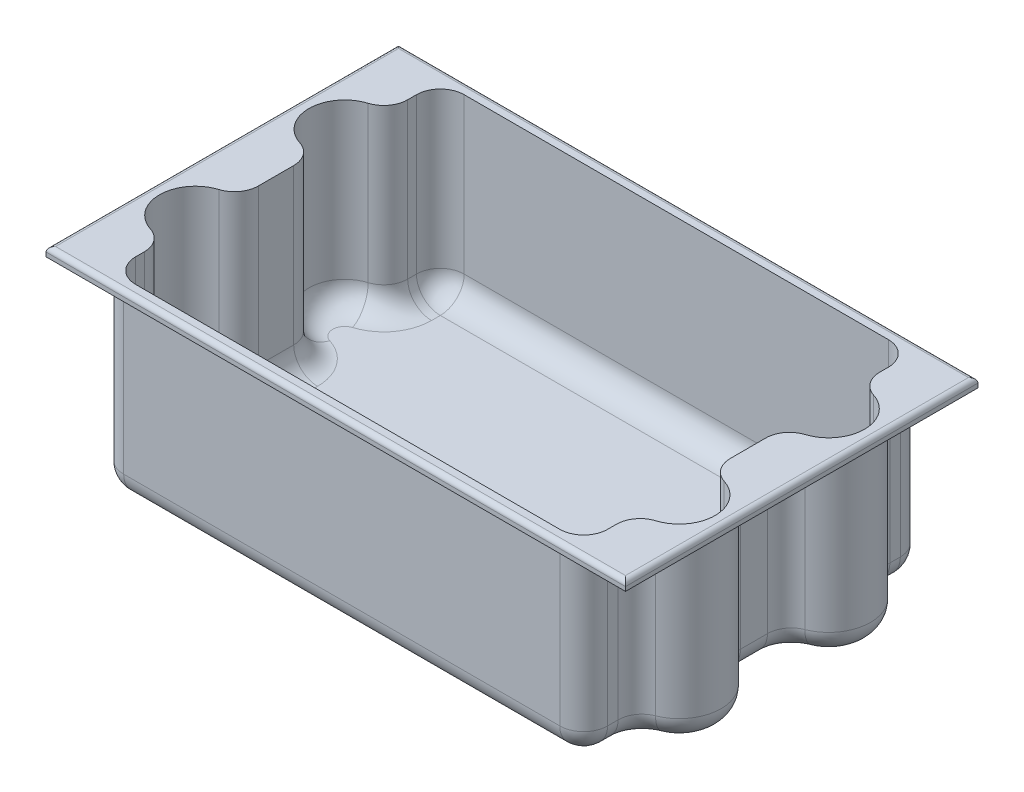
SolidWorks part; units mm, degrees
ref_plane "Front Plane" through (0, 0, 0) normal (0, 0, 1) x (1, 0, 0)
ref_plane "Top Plane" through (0, 0, 0) normal (0, 1, 0) x (1, 0, 0)
ref_plane "Right Plane" through (0, 0, 0) normal (1, 0, 0) x (0, 0, -1)
sketch "Sketch1" plane through (0, 0, 0) normal (0, 1, 0) x (1, 0, 0)
  line L0 (0, 0) -> (0, 50000) construction
  line L1 (-307.975, 187.325) -> (307.975, 187.325)
  line L2 (-307.975, 187.325) -> (-307.975, -187.325)
  line L3 (-307.975, -187.325) -> (307.975, -187.325)
  line L4 (307.975, 187.325) -> (307.975, -187.325)
  line L5 (0, -55) -> (0, 55) construction
  line L6 (0, 0) -> (50000, 0) construction
  line L7 (-55, 0) -> (55, 0) construction
  dimension "D1" = 615.95
  dimension "D2" = 374.65
extrude "Boss-Extrude1" add sketch "Sketch1" along normal blind 200.025
sketch "Sketch2" plane through (0, 0, 0) normal (0, -1, 0) x (1, 0, 0)
  line L0 (0, 0) -> (0, 50000) construction
  line L1 (-257.175, 174.625) -> (257.175, 174.625) construction
  line L2 (-257.175, 174.625) -> (-257.175, -174.625) construction
  line L3 (-257.175, -174.625) -> (257.175, -174.625) construction
  line L4 (257.175, 174.625) -> (257.175, -174.625) construction
  line L5 (0, -110.0137) -> (0, 110.0137) construction
  line L6 (0, 0) -> (50000, 0) construction
  line L7 (110.0137, 0) -> (-110.0137, 0) construction
  line L8 (-301.625, 187.325) -> (-301.625, -187.325) construction
  line L9 (-307.975, 187.325) -> (307.975, 187.325) construction
  line L10 (307.975, -187.325) -> (-307.975, -187.325) construction
  line L11 (-307.975, -187.325) -> (-307.975, 187.325) construction
  line L12 (-257.175, 123.825) -> (-257.175, 187.325)
  line L13 (-257.175, 187.325) -> (-307.975, 187.325)
  line L14 (-307.975, 187.325) -> (-307.975, -187.325)
  line L15 (-307.975, -187.325) -> (-257.175, -187.325)
  line L16 (-257.175, -187.325) -> (-257.175, -174.625)
  line L17 (-257.175, -174.625) -> (-257.175, -123.825)
  line L18 (-257.175, -34.925) -> (-257.175, 34.925)
  arc A0 (-257.175, 123.825) -> (-257.175, 34.925) centre (-257.175, 79.375) ccw
  arc A1 (-257.175, -123.825) -> (-257.175, -34.925) centre (-257.175, -79.375) cw
  dimension "D4" = 50.8
  dimension "D1" = 514.35
  dimension "D2" = 349.25
  dimension "D3" = 6.35
extrude "Cut-Extrude1" cut sketch "Sketch2" against normal blind 190.5
mirror "Mirror1" about plane through (0, 0, 0) normal (1, 0, 0) of "Cut-Extrude1"
sketch "Sketch3" plane through (0, 0, 0) normal (0, -1, 0) x (1, 0, 0)
  line L0 (257.175, 123.825) -> (257.175, 187.325) construction
  line L1 (-257.175, 187.325) -> (257.175, 187.325)
  line L2 (-257.175, 187.325) -> (-257.175, 180.975)
  line L3 (-257.175, 180.975) -> (257.175, 180.975)
  line L4 (257.175, 187.325) -> (257.175, 180.975)
  dimension "D1" = 6.35
extrude "Cut-Extrude2" cut sketch "Sketch3" against normal blind 190.5
mirror "Mirror2" about plane through (0, 0, 0) normal (0, 0, 1) of "Cut-Extrude2"
sketch "Sketch5" plane through (0, 200.025, 0) normal (0, 1, 0) x (1, 0, 0)
  line L58 (-250.825, 41.8079) -> (-250.825, -41.8079)
  line L59 (-250.825, 174.625) -> (-250.825, 116.9421)
  line L60 (250.825, 174.625) -> (-250.825, 174.625)
  line L61 (250.825, 116.9421) -> (250.825, 174.625)
  line L62 (250.825, -41.8079) -> (250.825, 41.8079)
  line L63 (250.825, -174.625) -> (250.825, -116.9421)
  line L64 (-250.825, -174.625) -> (250.825, -174.625)
  line L65 (-250.825, -116.9421) -> (-250.825, -174.625)
  line L66 (-250.825, 41.8079) -> (-250.825, -41.8079)
  line L67 (-250.825, 174.625) -> (-250.825, 116.9421)
  line L68 (250.825, 174.625) -> (-250.825, 174.625)
  line L69 (250.825, 116.9421) -> (250.825, 174.625)
  line L70 (250.825, -41.8079) -> (250.825, 41.8079)
  line L71 (250.825, -174.625) -> (250.825, -116.9421)
  line L72 (-250.825, -174.625) -> (250.825, -174.625)
  line L73 (-250.825, -116.9421) -> (-250.825, -174.625)
  arc A32 (-250.825, 116.9421) -> (-250.825, 41.8079) centre (-257.175, 79.375) ccw
  arc A33 (250.825, 41.8079) -> (250.825, 116.9421) centre (257.175, 79.375) ccw
  arc A34 (250.825, -116.9421) -> (250.825, -41.8079) centre (257.175, -79.375) ccw
  arc A35 (-250.825, -41.8079) -> (-250.825, -116.9421) centre (-257.175, -79.375) ccw
  arc A36 (-250.825, 116.9421) -> (-250.825, 41.8079) centre (-257.175, 79.375) ccw
  arc A37 (250.825, 41.8079) -> (250.825, 116.9421) centre (257.175, 79.375) ccw
  arc A38 (250.825, -116.9421) -> (250.825, -41.8079) centre (257.175, -79.375) ccw
  arc A39 (-250.825, -41.8079) -> (-250.825, -116.9421) centre (-257.175, -79.375) ccw
  dimension "D1" = 6.35
extrude "Cut-Extrude3" cut sketch "Sketch5" against normal blind 190.5
fillet "Fillet1" radius 25.4 12 edges at (257.175, 95.25, 180.975) (257.175, 95.25, 123.825) (257.175, 95.25, 34.925) (257.175, 95.25, -34.925) (257.175, 95.25, -123.825) (257.175, 95.25, -180.975) (-257.175, 95.25, -180.975) (-257.175, 95.25, -123.825) (-257.175, 95.25, 34.925) (-257.175, 95.25, -34.925) (-257.175, 95.25, 123.825) (-257.175, 95.25, 180.975)
fillet "Fillet2" radius 25.4 12 edges at (250.825, 104.775, -174.625) (-250.825, 104.775, -174.625) (-250.825, 104.775, -116.9421) (-250.825, 104.775, -41.8079) (-250.825, 104.775, 41.8079) (-250.825, 104.775, 116.9421) (-250.825, 104.775, 174.625) (250.825, 104.775, -116.9421) (250.825, 104.775, -41.8079) (250.825, 104.775, 41.8079) (250.825, 104.775, 174.625) (250.825, 104.775, 116.9421)
fillet "Fillet3" radius 25.4 24 edges at (-243.3855, 9.525, 167.1855) (-250.825, 9.525, 144.5876) (-255.7469, 9.525, 124.9233) (-295.275, 9.525, 79.375) (-255.7469, 9.525, 33.8267) (-250.825, 9.525, 0) (-255.7469, 9.525, -33.8267) (-295.275, 9.525, -79.375) (-255.7469, 9.525, -124.9233) (-250.825, 9.525, -144.5876) (-243.3855, 9.525, -167.1855) (0, 9.525, -174.625) (243.3855, 9.525, -167.1855) (250.825, 9.525, -144.5876) (255.7469, 9.525, -124.9233) (295.275, 9.525, -79.375) (255.7469, 9.525, -33.8267) (250.825, 9.525, 0) (255.7469, 9.525, 33.8267) (295.275, 9.525, 79.375) (255.7469, 9.525, 124.9233) (250.825, 9.525, 144.5876) (243.3855, 9.525, 167.1855) (0, 9.525, 174.625)
fillet "Fillet4" radius 25.4 24 edges at (257.175, 0, 150.0091) (261.6016, 0, 130.1156) (301.625, 0, 79.375) (261.6016, 0, 28.6344) (257.175, 0, 0) (261.6016, 0, -28.6344) (301.625, 0, -79.375) (261.6016, 0, -130.1156) (257.175, 0, -150.0091) (249.7355, 0, -173.5355) (0, 0, -180.975) (-249.7355, 0, -173.5355) (-257.175, 0, -150.0091) (-261.6016, 0, -130.1156) (-301.625, 0, -79.375) (-261.6016, 0, -28.6344) (-257.175, 0, 0) (-261.6016, 0, 28.6344) (-301.625, 0, 79.375) (-261.6016, 0, 130.1156) (-257.175, 0, 150.0091) (-249.7355, 0, 173.5355) (0, 0, 180.975) (249.7355, 0, 173.5355)
fillet "Fillet5" radius 5.08 4 edges at (-307.975, 200.025, 0) (0, 200.025, 187.325) (307.975, 200.025, 0) (0, 200.025, -187.325)
